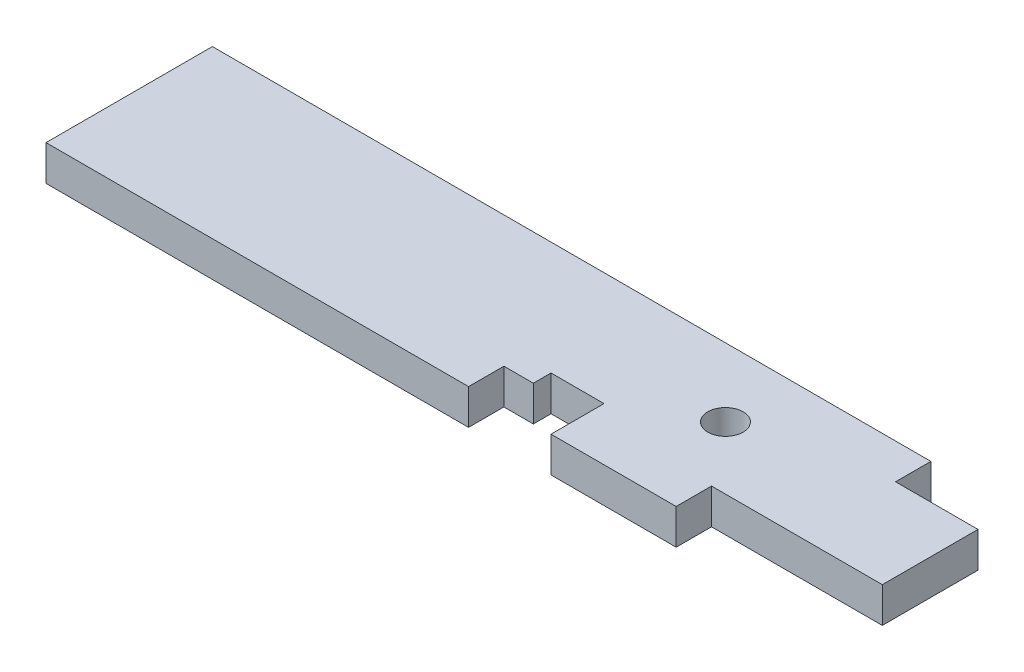
SolidWorks part; units mm, degrees
material "Pine"
ref_plane "Front Plane" through (0, 0, 0) normal (0, 0, 1) x (1, 0, 0)
ref_plane "Top Plane" through (0, 0, 0) normal (0, 1, 0) x (1, 0, 0)
ref_plane "Right Plane" through (0, 0, 0) normal (1, 0, 0) x (0, 0, -1)
sketch "Sketch1" plane through (0, 0, 0) normal (0, 1, 0) x (1, 0, 0)
  line L1 (0, 0) -> (774.7, 0)
  line L2 (0, 0) -> (0, -179.3875)
  line L3 (0, -179.3875) -> (863.6, -179.3875)
  line L4 (863.6, -38.1) -> (863.6, -179.3875)
  line L6 (774.7, 0) -> (774.7, -38.1)
  line L7 (774.7, -38.1) -> (863.6, -38.1)
  circle A0 centre (627.126, -73.914) radius 19.05
  dimension "D7" = 38.1
  dimension "D1" = 179.3875
  dimension "D2" = 774.7
  dimension "D3" = 863.6
  dimension "D4" = 38.1
  dimension "D5" = 627.126
  dimension "D6" = 73.914
extrude "Boss-Extrude1" add sketch "Sketch1" along normal blind 38.1
sketch "Sketch7" plane through (0, 38.1, 0) normal (0, 1, 0) x (1, 0, 0)
  line L8 (455.6125, -141.2875) -> (487.3625, -141.2875)
  line L9 (455.6125, -141.2875) -> (455.6125, -179.3875)
  line L10 (455.6125, -179.3875) -> (544.5125, -179.3875)
  line L12 (774.7, 0) -> (0, 0) construction
  line L13 (0, -179.3875) -> (863.6, -179.3875) construction
  line L18 (544.5125, -179.3875) -> (544.5125, -122.2375)
  line L19 (544.5125, -122.2375) -> (487.3625, -122.2375)
  line L20 (487.3625, -141.2875) -> (487.3625, -122.2375)
  dimension "D1" = 141.2875
  dimension "D2" = 455.6125
  dimension "D3" = 88.9
  dimension "D4" = 487.3625
  dimension "D5" = 122.2375
extrude "Cut-Extrude5" cut sketch "Sketch7" against normal through all
sketch "Sketch8" plane through (0, 38.1, 0) normal (0, 1, 0) x (1, 0, 0)
  line L1 (679.45, -179.3875) -> (863.6, -179.3875)
  line L2 (679.45, -179.3875) -> (679.45, -141.2748)
  line L3 (679.45, -141.2748) -> (863.6, -141.2748)
  line L4 (863.6, -179.3875) -> (863.6, -141.2748)
  line L5 (863.6, -179.3875) -> (863.6, -38.1) construction
  line L6 (0, -179.3875) -> (455.6125, -179.3875) construction
  dimension "D1" = 141.2748
  dimension "D2" = 679.45
extrude "Cut-Extrude6" cut sketch "Sketch8" against normal through all
